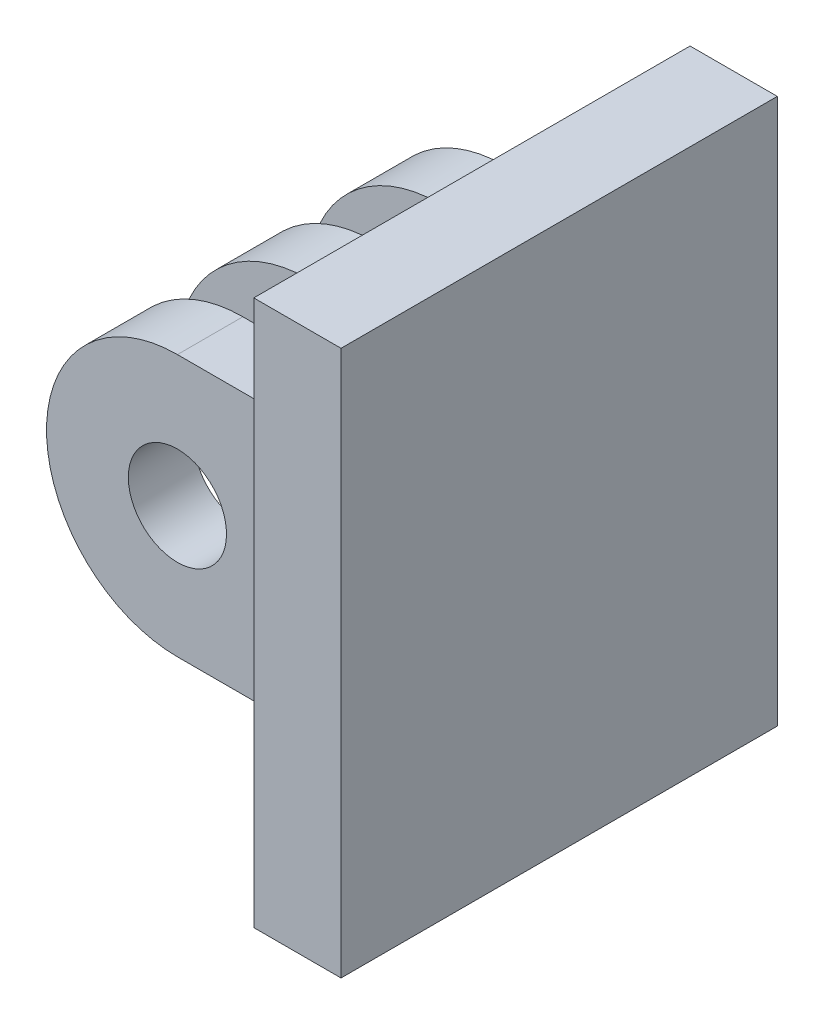
SolidWorks part; units mm, degrees
ref_plane "Front Plane" through (0, 0, 0) normal (0, 0, 1) x (1, 0, 0)
ref_plane "Top Plane" through (0, 0, 0) normal (0, 1, 0) x (1, 0, 0)
ref_plane "Right Plane" through (0, 0, 0) normal (1, 0, 0) x (0, 0, -1)
sketch "Sketch1" plane through (0, 0, 0) normal (1, 0, 0) x (0, 0, -1)
  line L1 (0, 0) -> (20, 0)
  line L2 (0, 0) -> (0, -25)
  line L3 (0, -25) -> (20, -25)
  line L4 (20, 0) -> (20, -25)
  dimension "D1" = 20
  dimension "D2" = 25
extrude "Boss-Extrude1" add sketch "Sketch1" along normal blind 4
sketch "Sketch2" plane through (0, 0, 0) normal (-1, 0, 0) x (0, 0, 1)
  line L0 (-10, 0) -> (-10, -25) construction
  line L1 (-20, 0) -> (0, 0) construction
  line L2 (0, -25) -> (-20, -25) construction
  line L3 (-20, -12.5) -> (0, -12.5) construction
  line L4 (-20, -25) -> (-20, 0) construction
  line L5 (0, 0) -> (0, -25) construction
  line L7 (-8.5, -18.5) -> (-11.5, -18.5)
  line L8 (-8.5, -18.5) -> (-8.5, -6.5)
  line L9 (-8.5, -6.5) -> (-11.5, -6.5)
  line L10 (-11.5, -18.5) -> (-11.5, -6.5)
  line L11 (-8.5, -18.5) -> (-11.5, -6.5) construction
  line L12 (-8.5, -6.5) -> (-11.5, -18.5) construction
  line L13 (-5.5, -6.5) -> (-2.5, -6.5)
  line L14 (-5.5, -6.5) -> (-5.5, -18.5)
  line L15 (-5.5, -18.5) -> (-2.5, -18.5)
  line L16 (-2.5, -6.5) -> (-2.5, -18.5)
  line L17 (-5.5, -6.5) -> (-2.5, -18.5) construction
  line L18 (-5.5, -18.5) -> (-2.5, -6.5) construction
  line L19 (-17.5, -6.5) -> (-14.5, -6.5)
  line L20 (-17.5, -6.5) -> (-17.5, -18.5)
  line L21 (-17.5, -18.5) -> (-14.5, -18.5)
  line L22 (-14.5, -6.5) -> (-14.5, -18.5)
  line L23 (-17.5, -6.5) -> (-14.5, -18.5) construction
  line L24 (-17.5, -18.5) -> (-14.5, -6.5) construction
  point P12 (-10, -12.5)
  point P17 (-4, -12.5)
  point P22 (-16, -12.5)
  dimension "D1" = 3
  dimension "D2" = 12
  dimension "D3" = 3
  dimension "D4" = 3
  dimension "D5" = 12
  dimension "D6" = 12
  dimension "D7" = 3
  dimension "D8" = 3
extrude "Boss-Extrude2" add sketch "Sketch2" along normal blind 12
sketch "Sketch3" plane through (0, 0, -17.5) normal (0, 0, -1) x (-1, 0, 0)
  line L0 (6, -6.5) -> (6, -18.5) construction
  line L1 (12, -6.5) -> (0, -6.5) construction
  line L2 (12, -18.5) -> (0, -18.5) construction
  line L3 (0, -12.5) -> (12, -12.5) construction
  line L4 (0, -25) -> (0, 0) construction
  line L5 (12, -6.5) -> (12, -18.5) construction
  line L6 (6, -6.5) -> (6, -5.4381)
  line L7 (6, -5.4381) -> (13.9218, -5.4381)
  line L8 (13.9218, -5.4381) -> (13.9218, -19.1631)
  line L9 (13.9218, -19.1631) -> (6, -19.1631)
  line L10 (6, -19.1631) -> (6, -18.5)
  circle A0 centre (6, -12.5) radius 2.25
  arc A1 (6, -6.5) -> (6, -18.5) centre (6, -12.5) cw
  point P12 (6, -12.5)
  line M9 (0, -18.5) -> (12, -18.5)
  line M10 (12, -18.5) -> (12, -6.5)
  line M11 (12, -6.5) -> (0, -6.5)
  dimension "D4" = 4.5
  dimension "D1" = 1.0619
  dimension "D2" = 7.9218
  dimension "D3" = 13.7251
extrude "Cut-Extrude1" cut sketch "Sketch3" against normal through all contours A0 | A1 M11 M10 | A1 M10 M9
chamfer "Chamfer1" distance 0.75 angle 45 1 edges at (-8.25, -12.5, -17.5)
